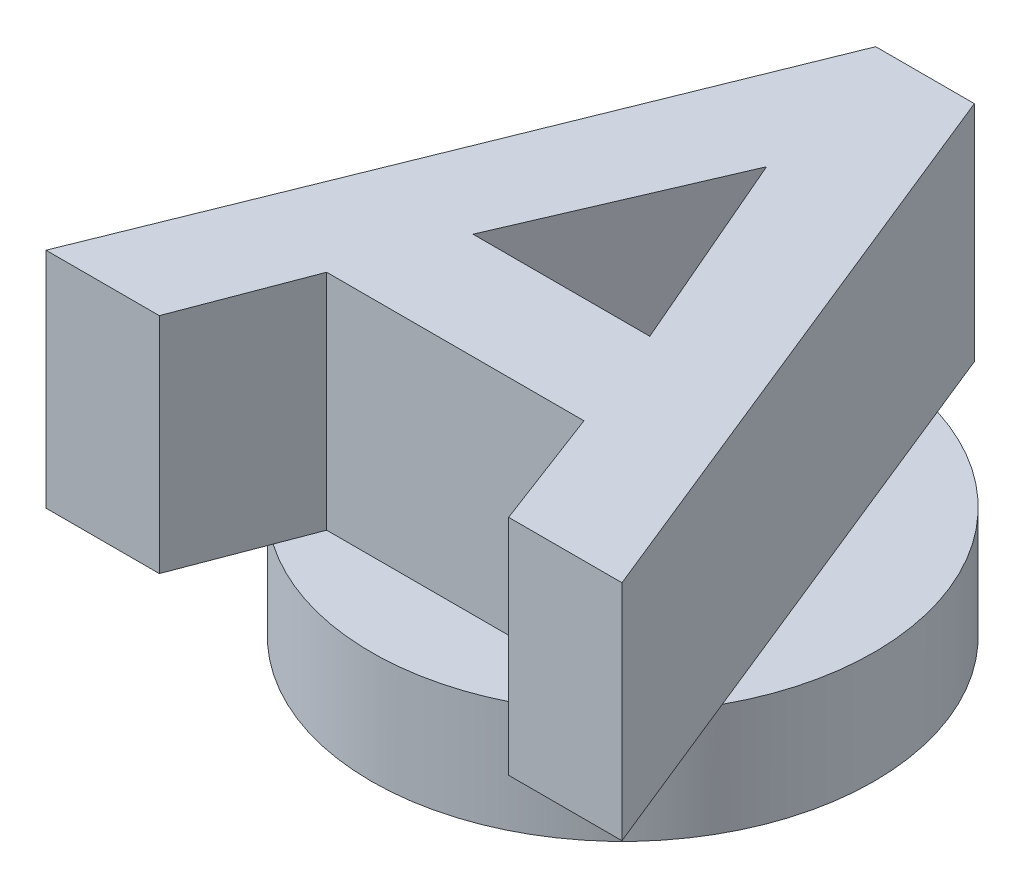
SolidWorks part; units mm, degrees
ref_plane "Front Plane" through (0, 0, 0) normal (0, 0, 1) x (1, 0, 0)
ref_plane "Top Plane" through (0, 0, 0) normal (0, 1, 0) x (1, 0, 0)
ref_plane "Right Plane" through (0, 0, 0) normal (1, 0, 0) x (0, 0, -1)
sketch "Sketch1" plane through (0, 0, 0) normal (0, 1, 0) x (1, 0, 0)
  circle A0 centre (0, 0) radius 22.5
  dimension "D1" = 45
extrude "Boss-Extrude1" add sketch "Sketch1" along normal blind 10
sketch "Sketch2" plane through (0, 10, 0) normal (0, 1, 0) x (1, 0, 0)
  text T0 "<b>A</b>\r\n" font "Century Gothic" height in points 200
extrude "Boss-Extrude2" add sketch "Sketch2" along normal blind 20
sketch "Sketch3" plane through (0, 0, 0) normal (0, -1, 0) x (1, 0, 0)
  line L0 (14.5514, 2.7786) -> (0, 30)
  line L1 (0, 30) -> (-14.5514, 2.7786)
  circle A0 centre (0, -5) radius 16.5
  circle A2 centre (0, 0) radius 22.5 construction
  circle A4 centre (0, 0) radius 21.5
  circle A5 centre (0, 0) radius 21.5
  dimension "D1" = 33
  dimension "D2" = 35
  dimension "D3" = 5
  dimension "D4" = 1
extrude "Cut-Extrude2" cut sketch "Sketch3" against normal blind 5 contours L0 A5 L1 A0 | A0
